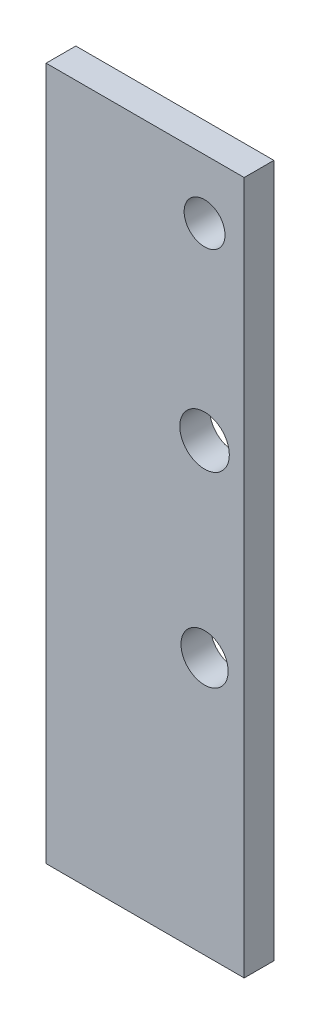
SolidWorks part; units mm, degrees
ref_plane "Plane1" through (0, 0, 0) normal (0, 0, 1) x (1, 0, 0)
ref_plane "Plane2" through (0, 0, 0) normal (0, 1, 0) x (1, 0, 0)
ref_plane "Plane3" through (0, 0, 0) normal (1, 0, 0) x (0, 0, -1)
sketch "Sketch1" plane through (0, 0, 0) normal (0, 1, 0) x (1, 0, 0)
  line L1 (0, 0) -> (100, 0)
  line L2 (0, 0) -> (0, 15)
  line L3 (0, 15) -> (100, 15)
  line L4 (100, 0) -> (100, 15)
  dimension "D1" = 15
  dimension "D2" = 100
extrude "Boss-Extrude1" add sketch "Sketch1" along normal blind 350
sketch "Sketch2" plane through (0, 0, 0) normal (0, 0, 1) x (1, 0, 0)
  line L0 (0, 350) -> (100, 350) construction
  line L2 (100, 350) -> (100, 0) construction
  circle A0 centre (80, 225) radius 12.5
  dimension "D3" = 25
  dimension "D1" = 125
  dimension "D2" = 20
extrude "Cut-Extrude1" cut sketch "Sketch2" against normal through all
sketch "Sketch3" plane through (0, 0, 0) normal (0, 0, 1) x (1, 0, 0)
  line L0 (0, 350) -> (100, 350) construction
  line L1 (100, 350) -> (100, 0) construction
  circle A0 centre (80, 320) radius 10.3185
  circle A1 centre (80, 130) radius 11.9071
  circle A3 centre (80, 225) radius 12.5 construction
  dimension "D2" = 95
  dimension "D3" = 20
  dimension "D1" = 30
  dimension "D4" = 20
extrude "Cut-Extrude2" cut sketch "Sketch3" against normal through all
